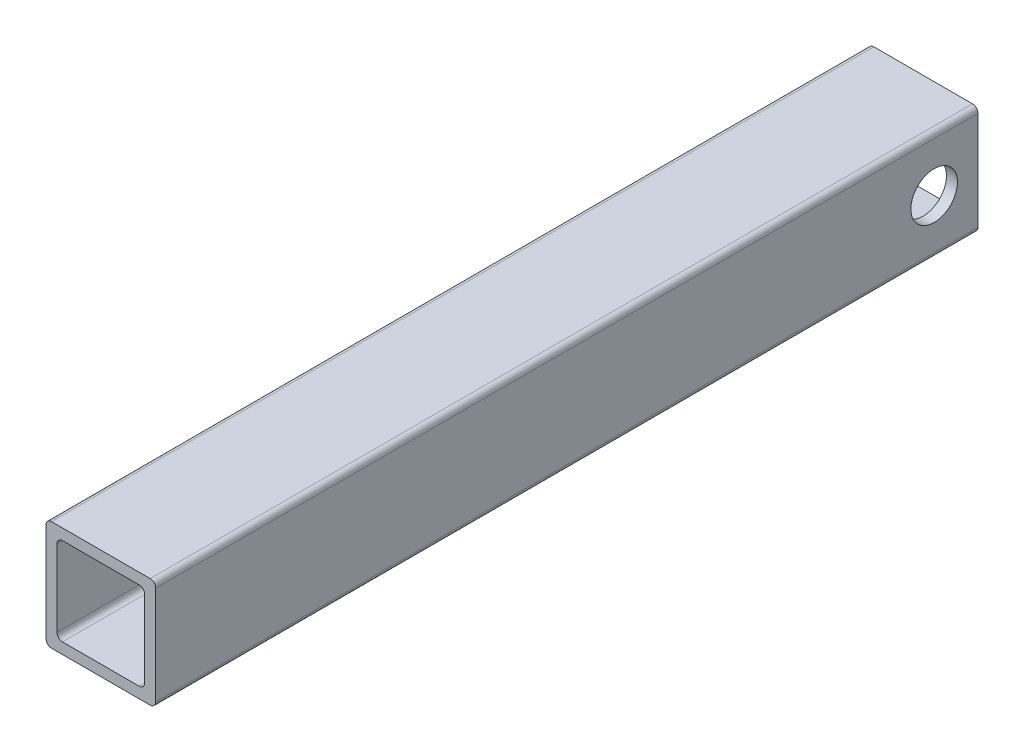
SolidWorks part; units mm, degrees
material "1.0037 (S235JR)"
ref_plane "Front Plane" through (0, 0, 0) normal (0, 0, 1) x (1, 0, 0)
ref_plane "Top Plane" through (0, 0, 0) normal (0, 1, 0) x (1, 0, 0)
ref_plane "Right Plane" through (0, 0, 0) normal (1, 0, 0) x (0, 0, -1)
sketch "Sketch1" plane through (0, 0, 0) normal (0, 0, 1) x (1, 0, 0)
  line L1 (-9, 10) -> (9, 10)
  line L2 (-10, 9) -> (-10, -9)
  line L3 (-9, -10) -> (9, -10)
  line L4 (10, 9) -> (10, -9)
  line L5 (-10, 10) -> (10, -10) construction
  line L6 (-10, -10) -> (10, 10) construction
  line L7 (-7, 8) -> (7, 8)
  line L8 (-8, 7) -> (-8, -7)
  line L9 (-7, -8) -> (7, -8)
  line L10 (8, 7) -> (8, -7)
  line L11 (-8, 8) -> (8, -8) construction
  line L12 (-8, -8) -> (8, 8) construction
  arc A0 (7, -8) -> (8, -7) centre (7, -7) ccw
  arc A1 (7, 8) -> (8, 7) centre (7, 7) cw
  arc A2 (-7, 8) -> (-8, 7) centre (-7, 7) ccw
  arc A3 (-8, -7) -> (-7, -8) centre (-7, -7) ccw
  arc A4 (-10, -9) -> (-9, -10) centre (-9, -9) ccw
  arc A5 (9, -10) -> (10, -9) centre (9, -9) ccw
  arc A6 (9, 10) -> (10, 9) centre (9, 9) cw
  arc A7 (-9, 10) -> (-10, 9) centre (-9, 9) ccw
  point P0 (0, 0)
  point P6 (0, 0)
  dimension "D4" = 1
  dimension "D1" = 20
  dimension "D2" = 16
  dimension "D3" = 20
extrude "Boss-Extrude1" add sketch "Sketch1" along normal blind 150
sketch "Sketch2" plane through (10, 0, 0) normal (1, 0, 0) x (0, 0, -1)
  line L0 (0, -9) -> (0, 9) construction
  circle A0 centre (-8, 0) radius 4.25
  dimension "D1" = 8.5
  dimension "D2" = 8
extrude "Cut-Extrude1" cut sketch "Sketch2" against normal through all
